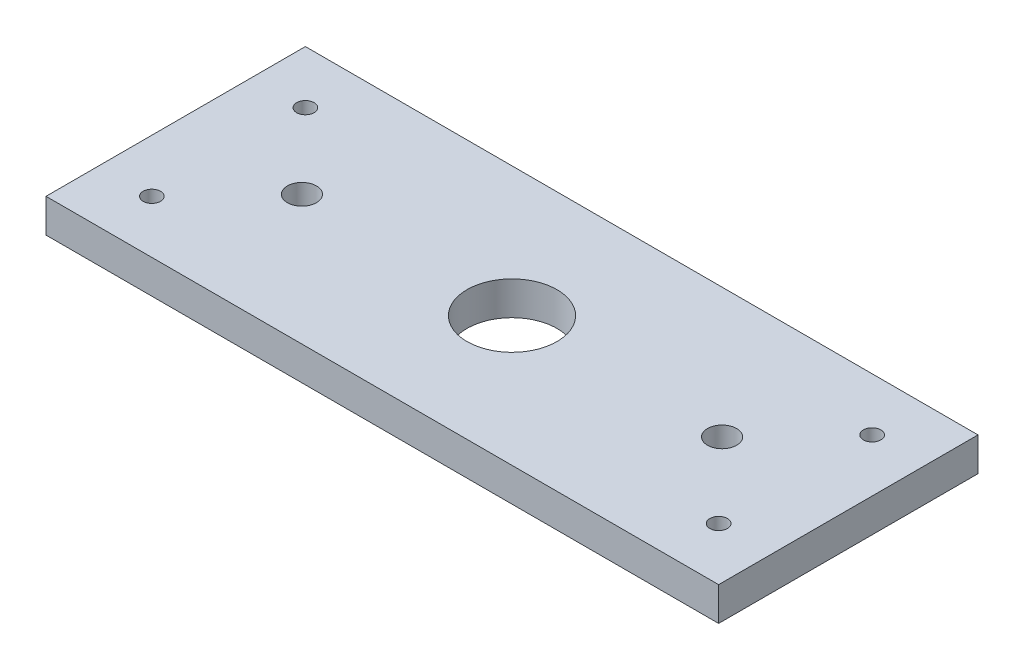
SolidWorks part; units mm, degrees
ref_plane "Front Plane" through (0, 0, 0) normal (0, 0, 1) x (1, 0, 0)
ref_plane "Top Plane" through (0, 0, 0) normal (0, 1, 0) x (1, 0, 0)
ref_plane "Right Plane" through (0, 0, 0) normal (1, 0, 0) x (0, 0, -1)
sketch "Sketch1" plane through (0, 0, 0) normal (0, 1, 0) x (1, 0, 0)
  line L0 (-63.5338, 24.5) -> (63.5338, -24.5) construction
  line L1 (-63.5338, 24.5) -> (63.5338, 24.5)
  line L2 (-63.5338, 24.5) -> (-63.5338, -24.5)
  line L3 (-63.5338, -24.5) -> (63.5338, -24.5)
  line L4 (63.5338, 24.5) -> (63.5338, -24.5)
  line L5 (-53.5338, -24.5) -> (-53.5338, -14.5) construction
  line L6 (-53.5338, -14.5) -> (-63.5338, -14.5) construction
  line L7 (-53.5338, 24.5) -> (-53.5338, 14.5) construction
  line L8 (-53.5338, 14.5) -> (-63.5338, 14.5) construction
  line L9 (0, -55) -> (0, 55) construction
  circle A0 centre (0, 0) radius 8.5
  circle A1 centre (-39.6875, 0) radius 2.75
  circle A3 centre (-53.5338, 14.5) radius 1.65
  circle A4 centre (-53.5338, -14.5) radius 1.65
  circle A5 centre (53.5338, 14.5) radius 1.65
  circle A6 centre (39.6875, 0) radius 2.75
  circle A7 centre (53.5338, -14.5) radius 1.65
  dimension "D1" = 17
  dimension "D2" = 5.5
  dimension "D3" = 3.3
  dimension "D4" = 10
  dimension "D5" = 107.0675
  dimension "D6" = 29
  dimension "D7" = 79.375
extrude "Boss-Extrude1" add sketch "Sketch1" along normal blind 6.35
